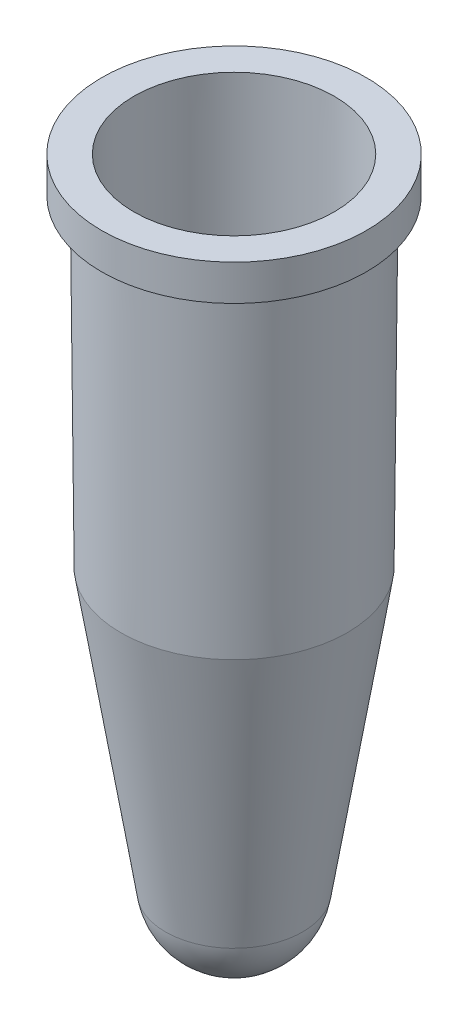
SolidWorks part; units mm, degrees
ref_plane "Front Plane" through (0, 0, 0) normal (0, 0, 1) x (1, 0, 0)
ref_plane "Top Plane" through (0, 0, 0) normal (0, 1, 0) x (1, 0, 0)
ref_plane "Right Plane" through (0, 0, 0) normal (1, 0, 0) x (0, 0, -1)
sketch "Sketch1" plane through (0, 0, 0) normal (0, 0, 1) x (1, 0, 0)
  line L0 (-5.6, 0) -> (-7.4, 0)
  line L1 (-7.4, 0) -> (-7.4, -2)
  line L2 (-7.4, -2) -> (-6.4826, -2)
  line L3 (-6.4826, -2) -> (-6.3255, -20)
  line L4 (-6.3255, -20) -> (-3.835, -35.7246)
  line L5 (0, 0) -> (0, -78.5552) construction
  line L6 (-5.5826, -1.9921) -> (-5.4261, -19.9253)
  line L7 (-5.4261, -19.9253) -> (-2.946, -35.5838)
  line L8 (-5.5826, -1.9921) -> (-5.6, 0)
  line L10 (5.5826, -1.9921) -> (5.6, 0)
  line L11 (5.6, 0) -> (7.4, 0)
  line L13 (6.4826, -2) -> (6.3255, -20)
  line L14 (5.5826, -1.9921) -> (5.4261, -19.9253)
  line L15 (5.4261, -19.9253) -> (2.946, -35.5838)
  line L16 (6.3255, -20) -> (3.835, -35.7246)
  line L17 (6.4826, -2) -> (6.4826, -11.7732) construction
  line L18 (6.4826, -2) -> (7.4, -2)
  line L35 (0, -38.1) -> (0, -39)
  line L36 (6.4826, -2) -> (6.4826, 0)
  line L41 (7.4, 0) -> (7.4, -2)
  arc A0 (-3.835, -35.7246) -> (3.835, -35.7246) centre (0, -35.1172) ccw
  arc A1 (-2.946, -35.5838) -> (2.946, -35.5838) centre (0, -35.1172) ccw
  arc A2 (-3.835, -35.7246) -> (-0.2847, -38.9895) centre (0, -35.1172) ccw construction
  arc A4 (-2.946, -35.5838) -> (-0.2187, -38.092) centre (0, -35.1172) ccw construction
  point P25 (0, -39)
  dimension "D1" = 0.9
  dimension "D2" = 2
  dimension "D3" = 20
  dimension "D4" = 11.2
  dimension "D5" = 14.8
  dimension "D6" = 39
  dimension "D7" = 0.5
  dimension "D8" = 9
revolve "Revolve25" add sketch "Sketch1" angle 360 about L5
scale "Scale1" bodies to scale 102 scale about centroid uniform scaling yes scale factor 0.857708
